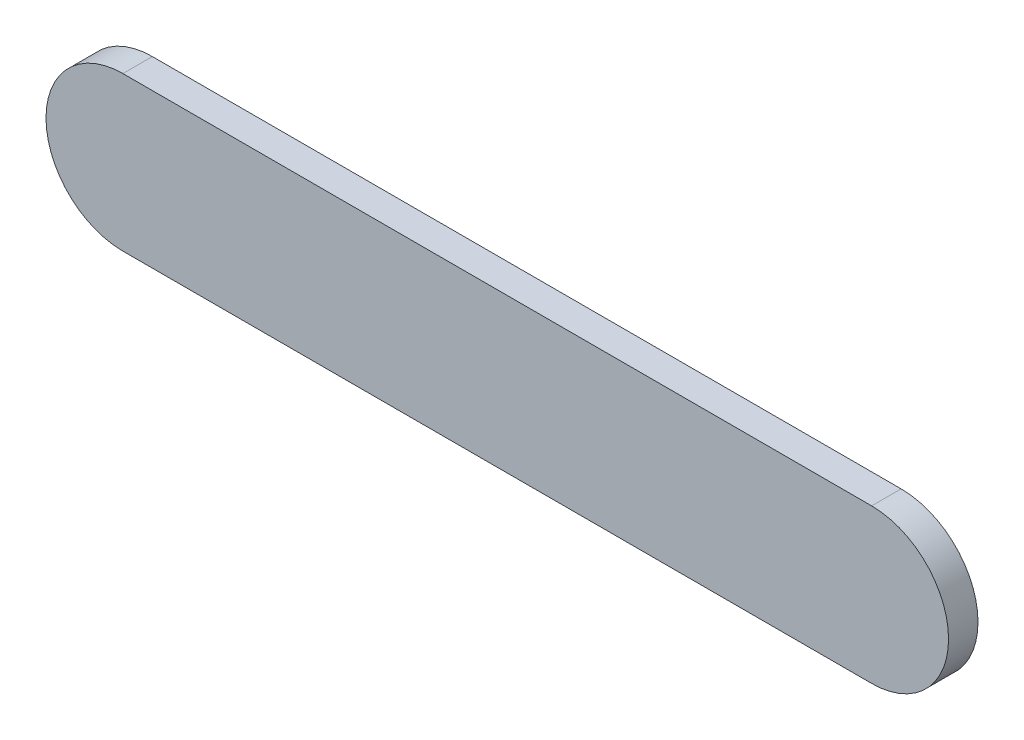
SolidWorks part; units mm, degrees
material "Caucho"
ref_plane "Alzado" through (0, 0, 0) normal (0, 0, 1) x (1, 0, 0)
ref_plane "Planta" through (0, 0, 0) normal (0, 1, 0) x (1, 0, 0)
ref_plane "Vista lateral" through (0, 0, 0) normal (1, 0, 0) x (0, 0, -1)
sketch "Croquis1" plane through (0, 0, 0) normal (0, 0, 1) x (1, 0, 0)
  line L0 (0, 0) -> (305, 0) construction
  line L10 (-22.5, -22.5) -> (327.5, -22.5) construction
  line L11 (-22.5, -22.5) -> (-22.5, 22.5) construction
  line L12 (-22.5, 22.5) -> (327.5, 22.5) construction
  line L13 (327.5, -22.5) -> (327.5, 22.5) construction
  line L14 (-22.5, -22.5) -> (327.5, 22.5) construction
  line L15 (-22.5, 22.5) -> (327.5, -22.5) construction
  line L23 (0, 15.66) -> (152.5, 15.66)
  line L24 (0, -15.66) -> (152.5, -15.66)
  arc A2 (152.5, -15.66) -> (152.5, 15.66) centre (152.5, 0) ccw
  circle A3 centre (152.5, 0) radius 15.66 construction
  circle A11 centre (0, 0) radius 15.66 construction
  arc A13 (0, 15.66) -> (0, -15.66) centre (0, 0) ccw
  point P1 (152.5, 0)
  point P7 (152.0383, 15.66)
  point P13 (151.9705, -15.66)
  point P14 (0.4888, -15.66)
  point P17 (0.4886, 15.66)
  dimension "D2" = 31.32
  dimension "D6" = 31.32
  dimension "D4" = 15.66
  dimension "D1" = 305
  dimension "D5" = 350
  dimension "D7" = 45
extrude "Saliente-Extruir1" add sketch "Croquis1" along normal blind 6
